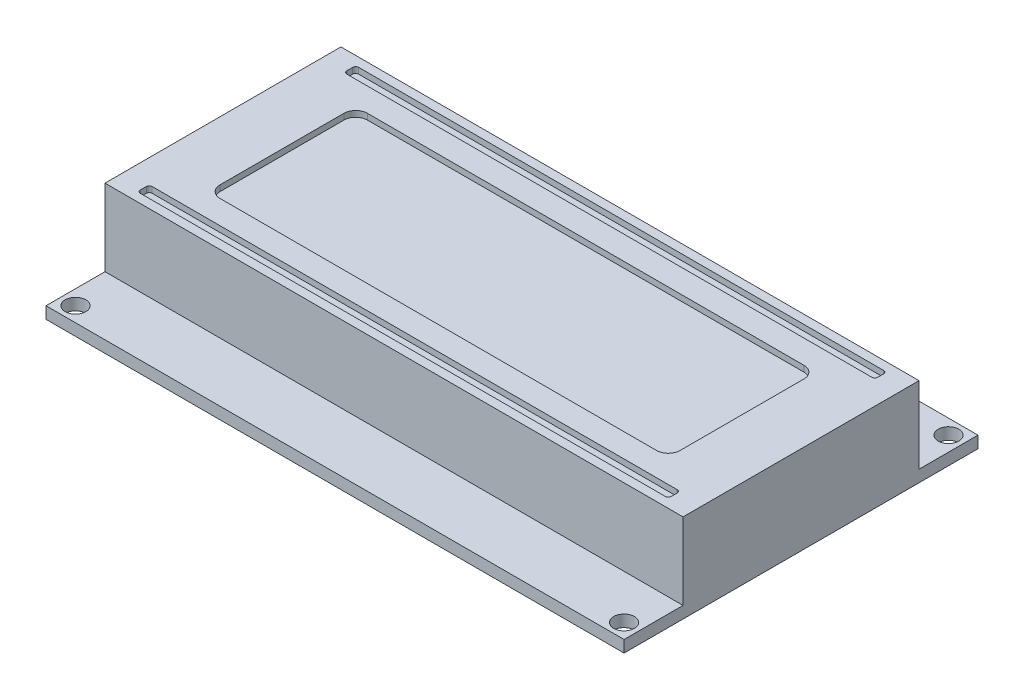
SolidWorks part; units mm, degrees
ref_plane "Front Plane" through (0, 0, 0) normal (0, 0, 1) x (1, 0, 0)
ref_plane "Top Plane" through (0, 0, 0) normal (0, 1, 0) x (1, 0, 0)
ref_plane "Right Plane" through (0, 0, 0) normal (1, 0, 0) x (0, 0, -1)
sketch "Sketch1" plane through (0, 0, 0) normal (0, 1, 0) x (1, 0, 0)
  line L0 (75, 55) -> (75, 0) construction
  line L1 (0, 0) -> (150, 0)
  line L2 (0, 0) -> (0, 55)
  line L3 (0, 55) -> (150, 55)
  line L4 (150, 0) -> (150, 55)
  line L5 (0, 27.5) -> (150, 27.5) construction
  circle A0 centre (3, 52) radius 1.5
  circle A1 centre (147, 52) radius 1.5
  circle A2 centre (147, 3) radius 1.5
  circle A3 centre (3, 3) radius 1.5
  dimension "D3" = 3
  dimension "D1" = 55
  dimension "D2" = 150
  dimension "D4" = 3
  dimension "D5" = 3
extrude "Boss-Extrude1" add sketch "Sketch1" along normal blind 2
sketch "Sketch2" plane through (0, 2, 0) normal (0, 1, 0) x (1, 0, 0)
  line L0 (0, 0) -> (150, 0) construction
  line L1 (0, 0) -> (0, 55) construction
  circle A0 centre (13, 10) radius 6
  dimension "D1" = 12
  dimension "D2" = 10
  dimension "D3" = 13
extrude "Boss-Extrude2" add sketch "Sketch2" along normal blind 10
sketch "Sketch3" plane through (0, 2, 0) normal (0, 1, 0) x (1, 0, 0)
  line L0 (0, 27.5) -> (150, 27.5) construction
  line L1 (7, 33.5) -> (19, 33.5)
  line L2 (7, 33.5) -> (7, 21.5)
  line L3 (7, 21.5) -> (19, 21.5)
  line L4 (19, 33.5) -> (19, 21.5)
  line L5 (13, 0) -> (13, 55) construction
  line L6 (0, 0) -> (150, 0) construction
  line L7 (0, 55) -> (150, 55) construction
  line L8 (7, 27.5) -> (19, 27.5) construction
  circle A1 centre (13, 10) radius 6 construction
  point P4 (7, 27.5)
  point P16 (13, 27.5)
  point P19 (13, 16)
  dimension "D1" = 12
  dimension "D2" = 12
extrude "Boss-Extrude3" add sketch "Sketch3" along normal blind 25
sketch "Sketch4" plane through (0, 2, 0) normal (0, 1, 0) x (1, 0, 0)
  line L0 (13, 45.5) -> (13, 40.5) construction
  line L1 (10.5, 45.5) -> (15.5, 45.5)
  line L2 (10.5, 45.5) -> (10.5, 40.5)
  line L3 (10.5, 40.5) -> (15.5, 40.5)
  line L4 (15.5, 45.5) -> (15.5, 40.5)
  line L5 (10.5, 43) -> (15.5, 43) construction
  line L7 (13, 0) -> (13, 55) construction
  line L8 (7, 33.5) -> (19, 33.5) construction
  line L9 (150, 0) -> (150, 55) construction
  line L10 (127, 8) -> (86, 8)
  line L11 (127, 8) -> (127, 5)
  line L12 (127, 5) -> (86, 5)
  line L13 (86, 8) -> (86, 5)
  line L14 (0, 0) -> (150, 0) construction
  point P8 (13, 43)
  dimension "D1" = 5
  dimension "D2" = 5
  dimension "D3" = 7
  dimension "D4" = 23
  dimension "D5" = 41
  dimension "D6" = 3
  dimension "D7" = 5
extrude "Boss-Extrude4" add sketch "Sketch4" along normal blind 5
sketch "Sketch5" plane through (0, 7, 0) normal (0, 1, 0) x (1, 0, 0)
  line L0 (86, 5) -> (127, 5) construction
  line L1 (86, 8) -> (127, 8)
  line L2 (86, 8) -> (86, 5)
  line L3 (86, 5) -> (127, 5)
  line L4 (127, 8) -> (127, 5)
  line L5 (86, 5) -> (127, 5) construction
  line L6 (10.5, 43) -> (15.5, 43) construction
  line L7 (10.5, 45.5) -> (10.5, 40.5) construction
  line L8 (15.5, 40.5) -> (15.5, 45.5) construction
  line L10 (10.5, 45.5) -> (15.5, 45.5)
  line L11 (10.5, 45.5) -> (10.5, 40.5)
  line L12 (10.5, 40.5) -> (15.5, 40.5)
  line L13 (15.5, 45.5) -> (15.5, 40.5)
  circle A0 centre (13, 43) radius 1.5
  point P15 (13, 43)
  dimension "D1" = 3
extrude "Cut-Extrude1" cut sketch "Sketch5" against normal blind 2
sketch "Sketch6" plane through (0, 27, 0) normal (0, 1, 0) x (1, 0, 0)
  line L0 (10.3706, 26.0556) -> (15.6294, 26.0556)
  line L1 (7, 33.5) -> (19, 33.5)
  line L2 (7, 33.5) -> (7, 21.5)
  line L3 (7, 21.5) -> (19, 21.5)
  line L4 (19, 33.5) -> (19, 21.5)
  arc A0 (15.6294, 26.0556) -> (10.3706, 26.0556) centre (13, 27.5) ccw
  dimension "D1" = 6
extrude "Cut-Extrude2" cut sketch "Sketch6" against normal blind 13
sketch "Sketch7" plane through (0, 14, 0) normal (0, 1, 0) x (1, 0, 0)
  line L1 (7, 33.5) -> (19, 33.5)
  line L2 (7, 33.5) -> (7, 21.5)
  line L3 (7, 21.5) -> (19, 21.5)
  line L4 (19, 33.5) -> (19, 21.5)
  circle A0 centre (13, 27.5) radius 3.5
  line M4 (7, 33.5) -> (7, 21.5)
  line M5 (7, 21.5) -> (19, 21.5)
  line M6 (19, 21.5) -> (19, 33.5)
  line M7 (19, 33.5) -> (7, 33.5)
  dimension "D1" = 7
extrude "Cut-Extrude3" cut sketch "Sketch7" against normal blind 7 contours A0 M7 M4 M5 M6
sketch "Sketch8" plane through (0, 12, 0) normal (0, 1, 0) x (1, 0, 0)
  circle A0 centre (13, 10) radius 1.25
  point P0 (13, 10)
  dimension "D1" = 2.5
extrude "Cut-Extrude4" cut sketch "Sketch8" against normal blind 5
sketch "Sketch9" plane through (0, 0, 0) normal (0, -1, 0) x (1, 0, 0)
  line L0 (0, -55) -> (150, -55) construction
  line L1 (149, -20) -> (131, -20)
  line L2 (149, -20) -> (149, -47)
  line L3 (149, -47) -> (124, -47)
  line L4 (124, -22) -> (124, -47)
  line L5 (150, 0) -> (150, -55) construction
  line L6 (124, -22) -> (129, -22)
  line L7 (129, -22) -> (131, -20)
  dimension "D1" = 8
  dimension "D2" = 27
  dimension "D3" = 1
  dimension "D4" = 25
  dimension "D5" = 2
  dimension "D6" = 5
  dimension "D7" = 45
extrude "Boss-Extrude5" add sketch "Sketch9" along normal blind 3
sketch "Sketch10" plane through (149, 0, 0) normal (1, 0, 0) x (0, 0, -1)
  line L0 (20, -1.5) -> (47, -1.5) construction
  line L1 (20, -3) -> (20, 0) construction
  line L2 (47, -3) -> (47, 0) construction
  line L3 (33.5, -3) -> (33.5, 0) construction
  line L4 (47, -3) -> (20, -3) construction
  line L5 (0, 0) -> (55, 0) construction
  line L6 (33.5, -2.25) -> (33.5, -0.75) construction
  line L7 (21, -2.25) -> (46, -2.25)
  line L8 (21, -2.25) -> (21, -0.75)
  line L9 (21, -0.75) -> (46, -0.75)
  line L10 (46, -2.25) -> (46, -0.75)
  line L11 (21, -1.5) -> (46, -1.5) construction
  point P20 (33.5, -1.5)
  point P21 (33.5, -1.5)
  dimension "D1" = 1.5
  dimension "D2" = 25
extrude "Cut-Extrude5" cut sketch "Sketch10" against normal blind 18
sketch "Sketch11" plane through (0, 5, 0) normal (0, 1, 0) x (1, 0, 0)
  line L0 (0, 0) -> (150, 0) construction
  line L1 (136, 64) -> (38, 64)
  line L2 (136, 64) -> (136, 4)
  line L3 (136, 4) -> (38, 4)
  line L4 (38, 64) -> (38, 4)
  line L5 (150, 0) -> (150, 55) construction
  line L6 (87, 64) -> (87, 4) construction
  line L7 (38, 34) -> (136, 34) construction
  circle A0 centre (40.5, 61.5) radius 1.75
  circle A1 centre (133.5, 61.5) radius 1.75
  circle A2 centre (133.5, 6.5) radius 1.75
  circle A3 centre (40.5, 6.5) radius 1.75
  point P12 (87, 34)
  dimension "D5" = 3.5
  dimension "D1" = 98
  dimension "D2" = 60
  dimension "D3" = 4
  dimension "D4" = 14
  dimension "D6" = 2.5
  dimension "D7" = 2.5
extrude "Boss-Extrude6" add sketch "Sketch11" along normal blind 2
sketch "Sketch12" plane through (0, 7, 0) normal (0, 1, 0) x (1, 0, 0)
  line L0 (38, 34) -> (136, 34) construction
  line L1 (38, 54) -> (136, 54)
  line L2 (38, 54) -> (38, 14)
  line L3 (38, 14) -> (136, 14)
  line L4 (136, 54) -> (136, 14)
  dimension "D1" = 40
extrude "Boss-Extrude7" add sketch "Sketch12" along normal blind 13
sketch "Sketch13" plane through (0, 20, 0) normal (0, 1, 0) x (1, 0, 0)
  line L0 (87, 54) -> (87, 14) construction
  line L1 (136, 54) -> (38, 54) construction
  line L2 (38, 14) -> (136, 14) construction
  line L3 (38, 34) -> (136, 34) construction
  line L4 (38, 54) -> (38, 14) construction
  line L5 (136, 14) -> (136, 54) construction
  line L6 (87, 46.5) -> (87, 21.5) construction
  line L7 (50, 46.5) -> (124, 46.5)
  line L8 (48, 44.5) -> (48, 23.5)
  line L9 (50, 21.5) -> (124, 21.5)
  line L10 (126, 44.5) -> (126, 23.5)
  line L11 (87, 52.5) -> (87, 50.5) construction
  line L12 (42.5, 52.5) -> (131.5, 52.5)
  line L13 (42, 52) -> (42, 51)
  line L14 (42.5, 50.5) -> (131.5, 50.5)
  line L15 (132, 52) -> (132, 51)
  line L16 (136, 54) -> (38, 54) construction
  line L17 (42, 52.5) -> (42, 50.5)
  line L18 (132, 52.5) -> (132, 50.5)
  line L19 (87, 15.5) -> (87, 17.5) construction
  line L20 (132, 16) -> (132, 17)
  line L21 (42, 16) -> (42, 17)
  line L22 (132, 15.5) -> (132, 17.5)
  line L23 (42.5, 17.5) -> (131.5, 17.5)
  line L24 (42, 15.5) -> (42, 17.5)
  line L25 (42.5, 15.5) -> (131.5, 15.5)
  arc A0 (131.5, 50.5) -> (132, 51) centre (131.5, 51) ccw
  arc A1 (131.5, 52.5) -> (132, 52) centre (131.5, 52) cw
  arc A2 (42, 51) -> (42.5, 50.5) centre (42.5, 51) ccw
  arc A3 (42.5, 52.5) -> (42, 52) centre (42.5, 52) ccw
  arc A4 (131.5, 15.5) -> (132, 16) centre (131.5, 16) ccw
  arc A5 (131.5, 17.5) -> (132, 17) centre (131.5, 17) cw
  arc A6 (42.5, 15.5) -> (42, 16) centre (42.5, 16) cw
  arc A7 (42.5, 17.5) -> (42, 17) centre (42.5, 17) ccw
  arc A8 (124, 46.5) -> (126, 44.5) centre (124, 44.5) cw
  arc A9 (48, 23.5) -> (50, 21.5) centre (50, 23.5) ccw
  arc A10 (50, 46.5) -> (48, 44.5) centre (50, 44.5) ccw
  arc A11 (124, 21.5) -> (126, 23.5) centre (124, 23.5) ccw
  point P18 (87, 34)
  point P19 (87, 34)
  point P62 (48, 21.5)
  point P65 (48, 46.5)
  dimension "D6" = 0.5
  dimension "D7" = 0.5
  dimension "D8" = 2
  dimension "D1" = 25
  dimension "D2" = 10
  dimension "D3" = 4
  dimension "D4" = 1.5
  dimension "D5" = 2
extrude "Cut-Extrude6" cut sketch "Sketch13" against normal blind 1 contours L15 L12 L13 L14 | L10 L7 L8 L9 | L21 L25 L20 L23
sketch "Sketch14" plane through (131, 0, 0) normal (1, 0, 0) x (0, 0, -1)
  line L1 (21, -0.75) -> (46, -0.75)
  line L2 (21, -0.75) -> (21, -2.25)
  line L3 (21, -2.25) -> (46, -2.25)
  line L4 (46, -0.75) -> (46, -2.25)
extrude "Boss-Extrude8" add sketch "Sketch14" along normal offset from surface (29 mm away) 11 up to face at (149, -1.5, -33.5) offset beyond the face yes
sketch "Sketch15" plane through (0, 2, 0) normal (0, 1, 0) x (1, 0, 0)
  line L1 (38, 64) -> (-8.6907, 64)
  line L2 (38, 64) -> (38, 4)
  line L3 (38, -2.9807) -> (-8.6907, -2.9807)
  line L4 (-8.6907, 64) -> (-8.6907, -2.9807)
  line L5 (38, 4) -> (136, 4)
  line L7 (38, -2.9807) -> (158.5564, -2.9807)
  line L8 (158.5564, 4) -> (158.5564, -2.9807)
  line L9 (158.5564, 4) -> (165.161, 4)
  line L10 (136, 4) -> (136, 64)
  line L11 (136, 64) -> (165.161, 64)
  line L12 (165.161, 4) -> (165.161, 64)
extrude "Cut-Extrude7" cut sketch "Sketch15" against normal blind 10 and the other way blind 76
sketch "Sketch16" plane through (0, 0, -4) normal (0, 0, 1) x (1, 0, 0)
  line L1 (38, 5) -> (136, 5)
  line L2 (38, 5) -> (38, -3)
  line L3 (38, -3) -> (136, -3)
  line L4 (136, 5) -> (136, -3)
extrude "Cut-Extrude8" cut sketch "Sketch16" against normal blind 69
